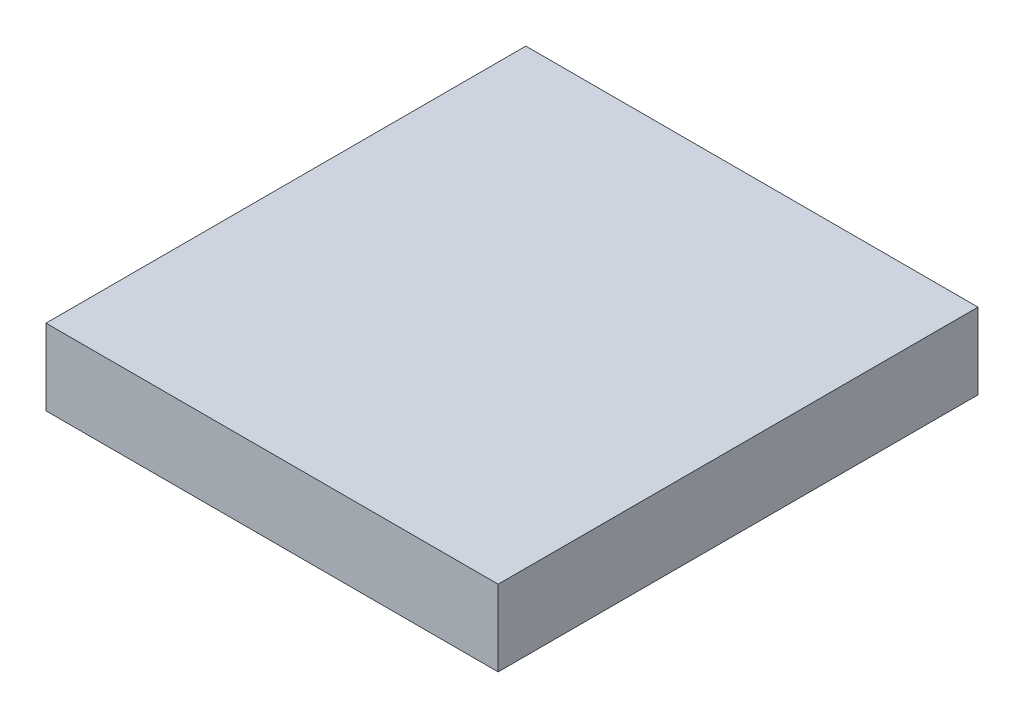
SolidWorks part; units mm, degrees
ref_plane "Спереди" through (0, 0, 0) normal (0, 0, 1) x (1, 0, 0)
ref_plane "Сверху" through (0, 0, 0) normal (0, 1, 0) x (1, 0, 0)
ref_plane "Справа" through (0, 0, 0) normal (1, 0, 0) x (0, 0, -1)
sketch "Эскиз1" plane through (0, 0, 0) normal (0, 1, 0) x (1, 0, 0)
  line L1 (0, 0) -> (238, 0)
  line L2 (0, 0) -> (0, 252.5805)
  line L3 (0, 252.5805) -> (238, 252.5805)
  line L4 (238, 0) -> (238, 252.5805)
extrude "Бобышка-Вытянуть1" add sketch "Эскиз1" along normal blind 40
